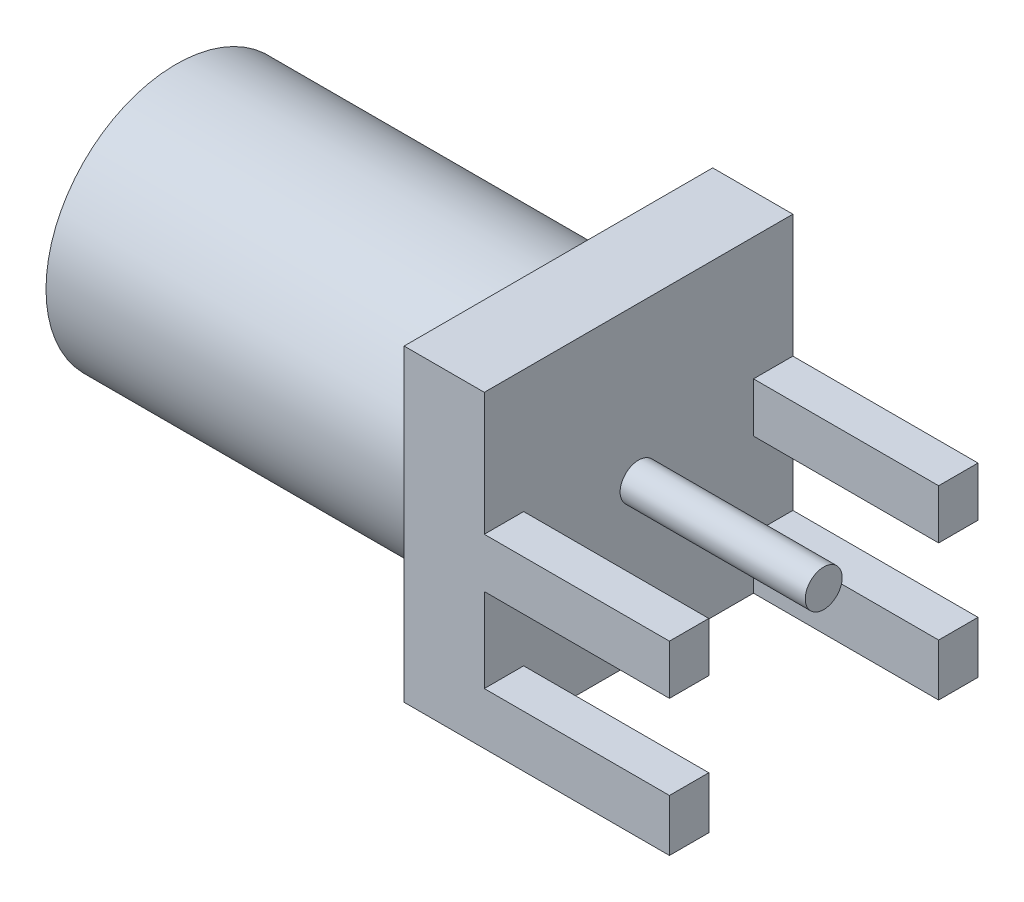
SolidWorks part; units mm, degrees
ref_plane "Front Plane" through (0, 0, 0) normal (0, 0, 1) x (1, 0, 0)
ref_plane "Top Plane" through (0, 0, 0) normal (0, 1, 0) x (1, 0, 0)
ref_plane "Right Plane" through (0, 0, 0) normal (1, 0, 0) x (0, 0, -1)
sketch "Sketch1" plane through (0, 0, 0) normal (1, 0, 0) x (0, 0, -1)
  line L1 (-3.175, -3.175) -> (3.175, -3.175)
  line L2 (-3.175, -3.175) -> (-3.175, 3.175)
  line L3 (-3.175, 3.175) -> (3.175, 3.175)
  line L4 (3.175, -3.175) -> (3.175, 3.175)
  line L5 (-3.175, -3.175) -> (3.175, 3.175) construction
  line L6 (-3.175, 3.175) -> (3.175, -3.175) construction
  point P0 (0, 0)
  dimension "D1" = 6.35
  dimension "D2" = 6.35
extrude "Boss-Extrude1" add sketch "Sketch1" against normal blind 1.65
sketch "Sketch2" plane through (0, 0, -3.175) normal (0, 0, -1) x (-1, 0, 0)
  line L0 (0, -3.175) -> (-3.81, -3.175)
  line L1 (-3.81, -3.175) -> (-3.81, -2.105)
  line L2 (-3.81, -2.105) -> (0, -2.105)
  line L3 (0, -3.175) -> (0, 3.175) construction
  line L4 (0, -2.105) -> (0, -3.175)
  line L5 (0, -0.375) -> (-3.81, -0.375)
  line L6 (-3.81, -0.375) -> (-3.81, 0.645)
  line L7 (-3.81, 0.645) -> (0, 0.645)
  line L8 (0, 0.645) -> (0, -0.375)
  dimension "D1" = 1.02
  dimension "D2" = 3.81
  dimension "D3" = 1.73
  dimension "D4" = 1.07
extrude "Boss-Extrude2" add sketch "Sketch2" against normal blind 0.81
mirror "Mirror1" about plane through (0, 0, 0) normal (0, 0, 1) of "Boss-Extrude2"
sketch "Sketch3" plane through (0, 0, 0) normal (1, 0, 0) x (0, 0, -1)
  circle A0 centre (0, 0) radius 0.38
  dimension "D1" = 0.76
extrude "Boss-Extrude3" add sketch "Sketch3" along normal up to surface (3.81 mm away) up to face at (3.81, 0.135, 2.77)
sketch "Sketch4" plane through (-1.65, 0, 0) normal (-1, 0, 0) x (0, 0, 1)
  circle A0 centre (0, 0) radius 2.675
  dimension "D1" = 5.35
extrude "Boss-Extrude4" add sketch "Sketch4" along normal offset from surface (7.87 mm away) 9.52 up to face at (0, -0.6253, 0.1731)
